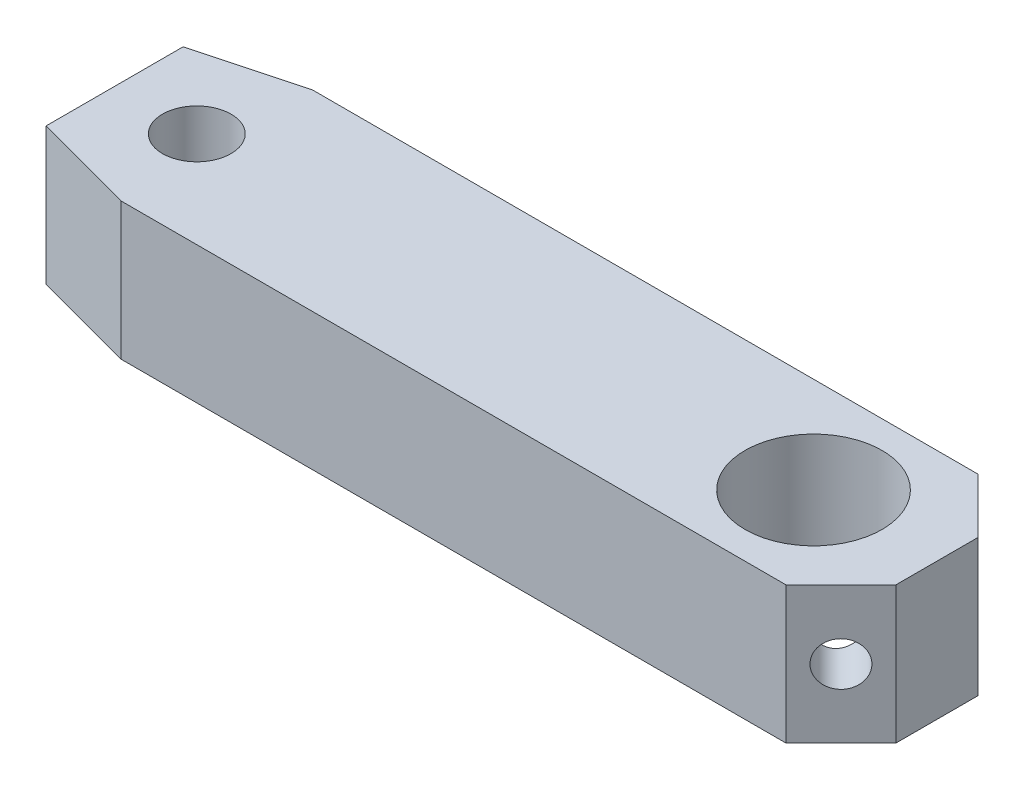
SolidWorks part; units mm, degrees
ref_plane "Front Plane" through (0, 0, 0) normal (0, 0, 1) x (1, 0, 0)
ref_plane "Top Plane" through (0, 0, 0) normal (0, 1, 0) x (1, 0, 0)
ref_plane "Right Plane" through (0, 0, 0) normal (1, 0, 0) x (0, 0, -1)
sketch "block" plane through (0, 0, 0) normal (0, 1, 0) x (1, 0, 0)
  line L0 (22.5, 0) -> (27, 3.5) construction
  line L1 (0.7321, 3.5) -> (25, 3.5)
  line L2 (-3, 2.5) -> (-3, -2.5)
  line L3 (0.7321, -3.5) -> (25, -3.5)
  line L4 (27, 1.5) -> (27, -1.5)
  line L5 (-3, 3.5) -> (27, -3.5) construction
  line L6 (-3, -3.5) -> (27, 3.5) construction
  line L7 (25, 3.5) -> (27, 1.5)
  line L8 (-3, -2.5) -> (0.7321, -3.5)
  line L9 (0.7321, 3.5) -> (-3, 2.5)
  line L10 (25, -3.5) -> (27, -1.5)
  circle A0 centre (22.5, 0) radius 2.5
  point P0 (0, 0)
  point P4 (12, 0)
  point P11 (26, 2.5)
  point P21 (26, -2.5)
  dimension "D2" = 5
  dimension "D1" = 22.5
  dimension "D3" = 0
  dimension "D4" = 0
  dimension "D5" = 3
  dimension "D6" = 4.5
  dimension "D7" = 3.5
  dimension "D8" = 24.741
  dimension "D9" = 2
  dimension "D10" = 45
  dimension "D11" = 1
  dimension "D12" = 75
  dimension "D13" = 1
  dimension "D14" = 75
  dimension "D15" = 2
  dimension "D16" = 45
extrude "Boss-Extrude1" add sketch "block" against normal blind 5 contours L1 L9 L2 L8 L3 L4 L7 A0
hole_wizard "M3 Tapped Hole1" positions "Sketch4" profile "Sketch5" tap size "M3" standard "ISO" end condition through all
sketch "Sketch4" plane through (0, 0, 0) normal (0, 1, 0) x (1, 0, 0)
  line L0 (0, -55) -> (0, 55) construction
  line L1 (-55, 0) -> (55, 0) construction
  point P0 (0, 0)
  dimension "D1" = 0
  dimension "D2" = 0
sketch "Sketch5" plane through (0, 0, 0) normal (1, 0, 0) x (0, 0, 1)
  line L0 (0, 0) -> (0, 5)
  line L1 (0, 5) -> (1.25, 5)
  line L2 (1.25, 5) -> (1.25, 0)
  line L5 (1.25, 0) -> (0, 0)
  line L11 (0, -6.35) -> (0, 107.95) construction
  dimension "Thru Tap Drill Dia." = 2.5
  dimension "Thru Tap Drill Depth" = 5
cosmetic thread "Hole Thread1" parameters "D2"=3
hole_wizard "M2 Tapped Hole1" positions "Sketch8" profile "Sketch9" tap size "M2" standard "ISO"
sketch "Sketch8" plane through (14.25, 0, -14.25) normal (0.7071, 0, -0.7071) x (-0.7071, 0, -0.7071)
  line L0 (-16.617, 0) -> (-16.617, -5) construction
  line L1 (-15.2028, 0) -> (-18.0312, 0) construction
  line L2 (-15.2028, -5) -> (-18.0312, -5) construction
  line L3 (-16.617, -5) -> (-16.617, -2.5) construction
  line L4 (-16.617, -2.5) -> (-18.0312, -2.5) construction
  line L5 (-18.0312, -5) -> (-18.0312, 0) construction
  point P0 (-16.617, -2.5)
  dimension "D1" = 0
  dimension "D2" = 0
sketch "Sketch9" plane through (26, -2.5, -2.5) normal (0, 1, 0) x (-0.7071, 0, -0.7071)
  line L0 (0, 0) -> (0, 1.8447)
  line L1 (0, 1.8447) -> (0.8, 1.8447)
  line L2 (0.8, 1.8447) -> (0.8, 0)
  line L5 (0.8, 0) -> (0, 0)
  line L11 (0, -6.35) -> (0, 107.95) construction
  dimension "Thru Tap Drill Dia." = 1.6
  dimension "Thru Tap Drill Depth" = 1.8447
cosmetic thread "Hole Thread3" parameters "D2"=2
mirror "Mirror1" about plane through (0, 0, 0) normal (0, 0, 1) of "M2 Tapped Hole1"
cosmetic thread "Hole Thread4" parameters "D2"=2
equation "\"D6@block\"=\"D2@block\" / 2 + 2"
equation "\"D7@block\" = \"D2@block\" / 2 + 1"
equation "\"D1@block\"=\"D2@block\"/2+20mm"
